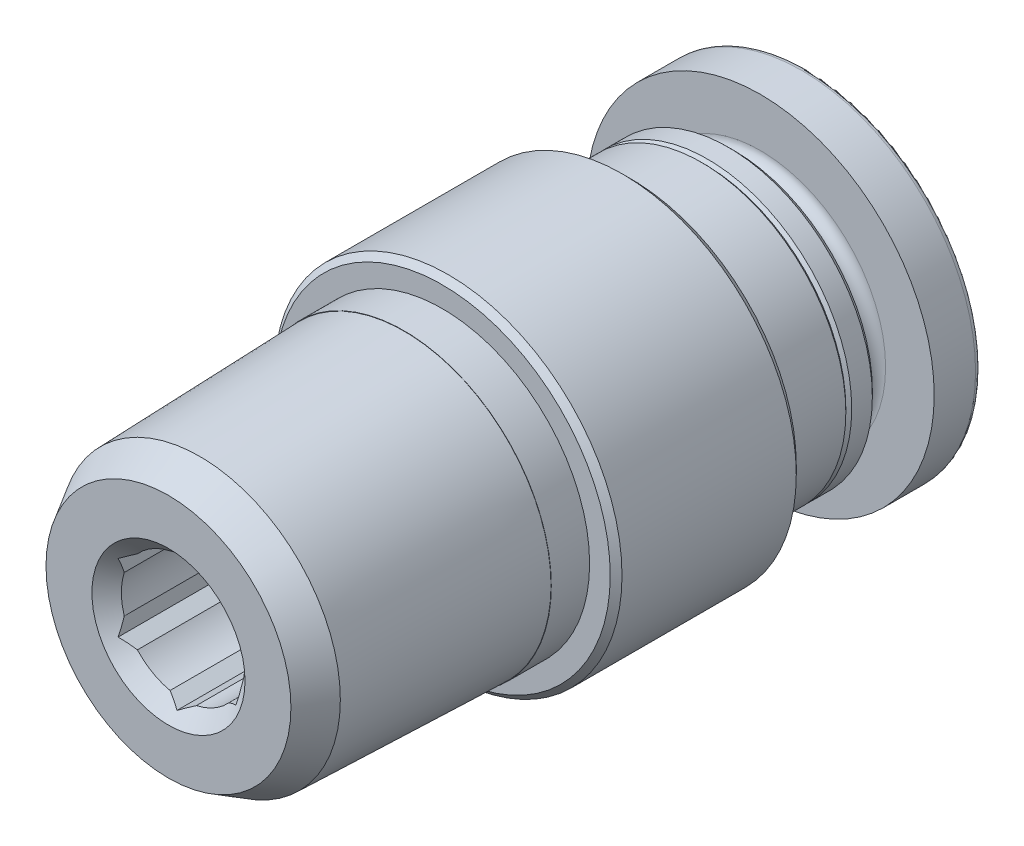
SolidWorks part; units mm, degrees
ref_plane "Front Plane" through (0, 0, 0) normal (0, 0, 1) x (1, 0, 0)
ref_plane "Top Plane" through (0, 0, 0) normal (0, 1, 0) x (1, 0, 0)
ref_plane "Right Plane" through (0, 0, 0) normal (1, 0, 0) x (0, 0, -1)
ref_plane "Plane1" through (0, 0, 0) normal (1, 0, 0) x (0, 0, -1)
sketch "Sketch1" plane through (0, 0, 0) normal (1, 0, 0) x (0, 0, -1)
  line L0 (0, 0) -> (0, 5.9)
  line L1 (0, 5.9) -> (7.4172, 5.9)
  line L2 (7.4172, 5.9) -> (7.7, 5.6172)
  line L3 (7.7, 5.6172) -> (7.7, 4.9)
  line L4 (7.7, 4.9) -> (10.1, 4.9)
  line L5 (10.1, 4.9) -> (10.2, 4.8)
  line L6 (10.2, 4.8) -> (10.3, 4.9)
  line L7 (10.3, 4.9) -> (11, 4.9)
  line L8 (11, 4.9) -> (11.2, 4.7)
  line L9 (11.2, 4.7) -> (11.2, 3.875)
  line L10 (11.2, 3.875) -> (11.725, 3.875)
  line L11 (12.1, 4.25) -> (12.1, 5.9)
  line L12 (12.1, 5.9) -> (13.5046, 5.9)
  line L13 (13.7015, 5.7347) -> (14.1, 3.475)
  line L14 (14.1, 3.475) -> (14.1, 0)
  line L15 (14.1, 0) -> (0, 0)
  line L16 (14.1, 0) -> (0, 0) construction
  arc A0 (11.725, 3.875) -> (12.1, 4.25) centre (11.725, 4.25) ccw
  arc A1 (13.5046, 5.9) -> (13.7015, 5.7347) centre (13.5046, 5.7) cw
revolve "Revolve1" add sketch "Sketch1" angle 360 about L16
ref_plane "Plane2" through (0, 0, 0) normal (1, 0, 0) x (0, 0, -1)
sketch "Sketch2" plane through (0, 0, 0) normal (1, 0, 0) x (0, 0, -1)
  line L0 (-8, 0) -> (-8, 4.1581)
  line L1 (-8, 4.1581) -> (-6.9362, 4.7723)
  line L2 (-6.9362, 4.7723) -> (0, 4.9889)
  line L3 (0, 4.9889) -> (0, 0)
  line L4 (0, 0) -> (-8, 0)
  line L5 (0, 0) -> (-8, 0) construction
revolve "Revolve2" add sketch "Sketch2" angle 360 about L5
ref_plane "Plane3" through (0, 0, 0) normal (1, 0, 0) x (0, 0, -1)
sketch "Sketch3" plane through (0, 0, 0) normal (1, 0, 0) x (0, 0, -1)
  line L0 (0, 5.9) -> (0, 5)
  line L1 (0, 5) -> (1.3, 5)
  line L2 (1.3, 5) -> (1.3, 5.7)
  line L3 (1.3, 5.7) -> (1.5, 5.9)
  line L4 (1.5, 5.9) -> (0, 5.9)
  line L5 (50, 0) -> (-50, 0) construction
revolve "Cut-Revolve1" cut sketch "Sketch3" angle 360 about L5
ref_plane "Plane4" through (0, 0, 0) normal (1, 0, 0) x (0, 0, -1)
sketch "Sketch4" plane through (0, 0, 0) normal (1, 0, 0) x (0, 0, -1)
  line L0 (-8, 0) -> (-8, 2.6)
  line L1 (-8, 2.6) -> (-7.5, 2.1)
  line L2 (-7.5, 2.1) -> (-2.9, 2.1)
  line L3 (-2.9, 2.1) -> (-2.9, 3.175)
  line L4 (-2.9, 3.175) -> (13.8, 3.175)
  line L5 (14.1, 3.475) -> (14.1, 0)
  line L6 (14.1, 0) -> (-8, 0)
  line L7 (14.1, 0) -> (-8, 0) construction
  arc A0 (13.8, 3.175) -> (14.1, 3.475) centre (13.8, 3.475) ccw
revolve "Cut-Revolve2" cut sketch "Sketch4" angle 360 about L7
ref_plane "Plane5" through (0, 0, 2.9) normal (0, 0, 1) x (1, 0, 0)
sketch "Sketch5" plane through (0, 0, 2.9) normal (0, 0, 1) x (1, 0, 0)
  line L0 (-2, -1.1547) -> (0, -2.3094)
  line L1 (0, -2.3094) -> (2, -1.1547)
  line L2 (2, -1.1547) -> (2, 1.1547)
  line L3 (2, 1.1547) -> (0, 2.3094)
  line L4 (0, 2.3094) -> (-2, 1.1547)
  line L5 (-2, 1.1547) -> (-2, -1.1547)
extrude "Cut-Extrude1" cut sketch "Sketch5" along normal blind 5.1
